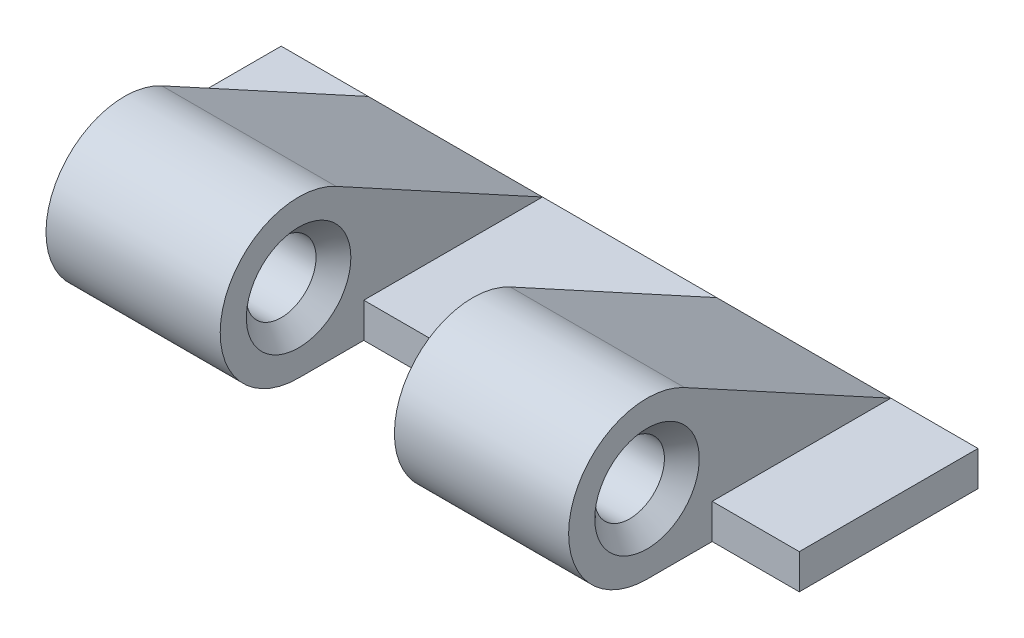
SolidWorks part; units mm, degrees
ref_plane "Ebene vorne" through (0, 0, 0) normal (0, 0, 1) x (1, 0, 0)
ref_plane "Ebene oben" through (0, 0, 0) normal (0, 1, 0) x (1, 0, 0)
ref_plane "Ebene rechts" through (0, 0, 0) normal (1, 0, 0) x (0, 0, -1)
sketch "Skizze2" plane through (0, 0, 0) normal (0, 1, 0) x (1, 0, 0)
  line L1 (-7.5, 3.5) -> (7.5, 3.5)
  line L2 (-7.5, 3.5) -> (-7.5, -3.5)
  line L3 (-7.5, -3.5) -> (7.5, -3.5)
  line L4 (7.5, 3.5) -> (7.5, -3.5)
  line L5 (-7.5, 3.5) -> (7.5, -3.5) construction
  line L6 (-7.5, -3.5) -> (7.5, 3.5) construction
  point P0 (0, 0)
  dimension "D1" = 15
  dimension "D2" = 7
extrude "Aufsatz-Linear austragen1" add sketch "Skizze2" along normal blind 1
sketch "Skizze3" plane through (7.5, 0, 0) normal (1, 0, 0) x (0, 0, -1)
  circle A0 centre (-3.5, 2.25) radius 2.25
  circle A1 centre (-3.5, 2.25) radius 1
  dimension "D1" = 2
  dimension "D2" = 4.5
extrude "Aufsatz-Linear austragen2" add sketch "Skizze3" against normal up to surface (15 mm away) up to face at (-7.5, 0.5, 0)
ref_plane "Tangential Ebene" through (0, 0, 1.25) normal (0, 0, -1) x (-1, 0, 0)
sketch "Skizze5" plane through (7.5, 0, 0) normal (1, 0, 0) x (0, 0, -1)
  line L0 (-1.6292, 1) -> (-1.6292, 0)
  line L1 (-1.6292, 0) -> (-3.5, 0)
  line L3 (3.5, 1) -> (-1.6292, 1)
  line L4 (-3.5, 0) -> (3.5, 0)
  line L5 (3.5, 0) -> (3.5, 1)
  line L6 (3.5, 1) -> (-1.6292, 1) construction
  line L7 (-3.5, 0) -> (3.5, 0) construction
  line L8 (3.5, 0) -> (3.5, 1) construction
  arc A1 (-1.6292, 1) -> (-3.5, 0) centre (-3.5, 2.25) ccw
  arc A2 (-1.6292, 1) -> (-3.5, 0) centre (-3.5, 2.25) ccw
  dimension "D1" = 0
extrude "Schnitt-Linear austragen1" cut sketch "Skizze5" against normal blind 5 from offset 5 offset against normal yes
ref_plane "Spiegelebene" through (0, 0, 0) normal (1, 0, 0) x (0, 0, -1)
sketch "Skizze7" plane through (7.5, 0, 0) normal (1, 0, 0) x (0, 0, -1)
  line L1 (-1.6292, 1) -> (3.5, 1)
  line L2 (-1.6292, 1) -> (-1.6292, 0)
  line L3 (-1.6292, 0) -> (3.5, 0)
  line L4 (3.5, 1) -> (3.5, 0)
extrude "Aufsatz-Linear austragen3" add sketch "Skizze7" along normal blind 2.5
mirror "Spiegeln1" about plane through (0, 0, 0) normal (1, 0, 0) of "Aufsatz-Linear austragen3"
chamfer "Fase1" distance 0.5 angle 45 4 edges at (-7.5, 2.25, 2.5) (-2.5, 2.25, 2.5) (2.5, 2.25, 2.5) (7.5, 2.25, 2.5)
sketch "Skizze8" plane through (7.5, 0, 0) normal (1, 0, 0) x (0, 0, -1)
  line L0 (-1.6292, 1) -> (3.5, 1)
  line L1 (3.5, 1) -> (-2.4239, 4.226)
  line L2 (-2.4239, 4.226) -> (-1.6292, 1)
  arc A0 (-1.6292, 1) -> (-3.5, 0) centre (-3.5, 2.25) ccw construction
extrude "Verstärkungsfase" add sketch "Skizze8" against normal up to surface (5 mm away) from surface at 0 up to face at (2.5, 2.25, 2) starting at face at (7.5, 2.25, 5)
sketch "Skizze9" plane through (-7.5, 0, 0) normal (-1, 0, 0) x (0, 0, 1)
  line L0 (1.6292, 1) -> (-3.5, 1)
  line L1 (-3.5, 1) -> (2.4239, 4.226)
  line L2 (2.4239, 4.226) -> (1.6292, 1)
  arc A0 (3.5, 0) -> (1.6292, 1) centre (3.5, 2.25) ccw construction
extrude "Aufsatz-Linear austragen5" add sketch "Skizze9" against normal up to surface (5 mm away) from surface at 0 up to face at (-2.5, 2.25, 2) starting at face at (-7.5, 2.25, 2)
